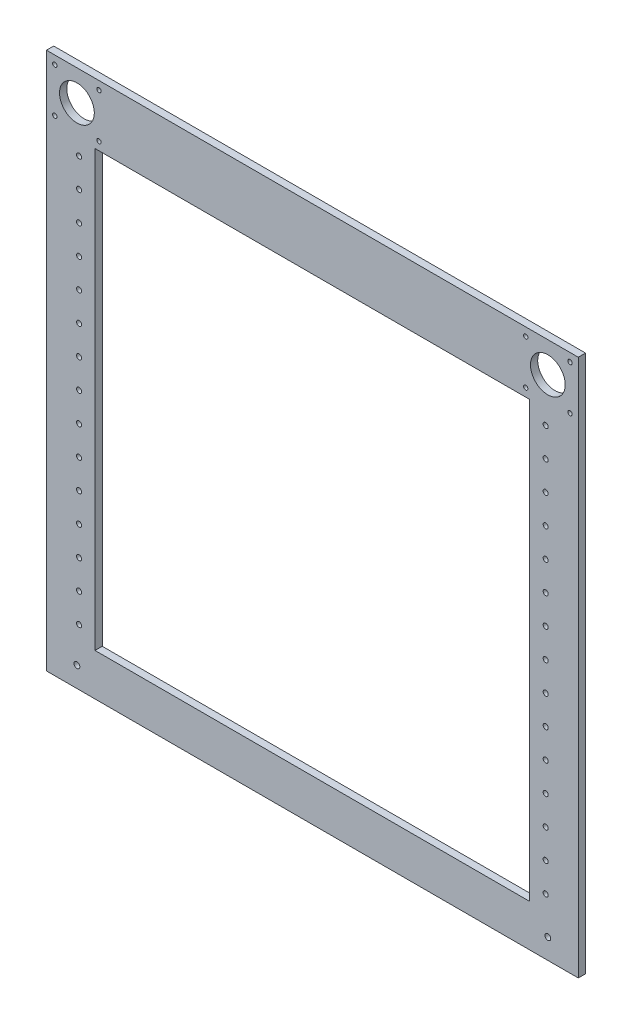
SolidWorks part; units mm, degrees
ref_plane "Front Plane" through (0, 0, 0) normal (0, 0, 1) x (1, 0, 0)
ref_plane "Top Plane" through (0, 0, 0) normal (0, 1, 0) x (1, 0, 0)
ref_plane "Right Plane" through (0, 0, 0) normal (1, 0, 0) x (0, 0, -1)
sketch "Sketch2" plane through (0, 0, -4) normal (0, 0, 1) x (1, 0, 0)
  line L1 (-7.5, -500) -> (-7.5, -200) construction
  line L2 (-307.5, -200) -> (-307.5, -500) construction
  line L4 (16, -158) -> (16, -529)
  line L5 (-7.5, -500) -> (-7.5, -200)
  line L6 (-307.5, -200) -> (-307.5, -500)
  line L7 (-331, -529) -> (-331, -158)
  line L8 (-7.5, -200) -> (-307.5, -200)
  line L9 (-7.5, -500) -> (-307.5, -500)
  line L10 (-331, -158) -> (16, -158)
  line L11 (-331, -529) -> (16, -529)
  dimension "D1" = 300
  dimension "D2" = 300
  dimension "D3" = 29
  dimension "D4" = 42
  dimension "D5" = 23.5
  dimension "D6" = 23.5
extrude "Boss-Extrude1" add sketch "Sketch2" along normal blind 5
sketch "Sketch3" plane through (0, 0, -4) normal (0, 0, -1) x (-1, 0, 0)
  line L4 (-16, -158) -> (-16, -529)
  line L5 (-16, -529) -> (331, -529)
  line L6 (331, -529) -> (331, -158)
  line L7 (331, -158) -> (-16, -158)
  line L8 (-16, -158) -> (-16, -529)
  line L9 (-16, -529) -> (331, -529)
  line L10 (331, -529) -> (331, -158)
  line L11 (331, -158) -> (-16, -158)
  circle A0 centre (320, -179) radius 12
  dimension "D2" = 24
  dimension "D1" = 0
sketch "Sketch6" plane through (0, 0, -4) normal (0, 0, -1) x (-1, 0, 0)
  circle A0 centre (318.5, -490) radius 1.75
  circle A1 centre (318.5, -470) radius 1.75
  circle A2 centre (318.5, -450) radius 1.75
  circle A3 centre (318.5, -430) radius 1.75
  circle A4 centre (318.5, -410) radius 1.75
  circle A5 centre (318.5, -390) radius 1.75
  circle A6 centre (318.5, -370) radius 1.75
  circle A7 centre (318.5, -350) radius 1.75
  circle A8 centre (318.5, -330) radius 1.75
  circle A9 centre (318.5, -310) radius 1.75
  circle A10 centre (318.5, -290) radius 1.75
  circle A11 centre (318.5, -270) radius 1.75
  circle A12 centre (318.5, -250) radius 1.75
  circle A13 centre (318.5, -230) radius 1.75
  circle A14 centre (318.5, -210) radius 1.75
  dimension "D1" = 15
extrude "Cut-Extrude1" cut sketch "Sketch6" against normal blind 10
ref_plane "Plane1" through (-157.5, 0, 0) normal (-1, 0, 0) x (0, 0, 1)
mirror "Mirror1" about plane through (-157.5, 0, 0) normal (-1, 0, 0) of "Cut-Extrude1"
sketch "Sketch7" plane through (0, 0, 1) normal (0, 0, 1) x (1, 0, 0)
  line L0 (-331, -529) -> (-331, -158) construction
  line L1 (-331, -529) -> (-331, -158)
  line L2 (-331, -158) -> (-341, -158)
  line L3 (-341, -158) -> (-341, -529)
  line L4 (-331, -529) -> (-341, -529)
  dimension "D1" = 10
extrude "Boss-Extrude2" add sketch "Sketch7" against normal blind 5
mirror "Mirror2" about plane through (-157.5, 0, 0) normal (-1, 0, 0) of "Boss-Extrude2"
extrude "Cut-Extrude2" cut sketch "Sketch3" against normal blind 5 contours A0
sketch "Sketch8" plane through (0, 0, 1) normal (0, 0, 1) x (1, 0, 0)
  line L4 (-341, -529) -> (26, -529)
  line L5 (26, -529) -> (26, -158)
  line L6 (26, -158) -> (-341, -158)
  line L7 (-341, -158) -> (-341, -529)
  line L8 (-341, -529) -> (26, -529)
  line L9 (26, -529) -> (26, -158)
  line L10 (26, -158) -> (-341, -158)
  line L11 (-341, -158) -> (-341, -529)
  dimension "D1" = 0
sketch "Sketch9" plane through (0, 0, -4) normal (0, 0, -1) x (-1, 0, 0)
  line L1 (304.7336, -163.7336) -> (335.2664, -163.7336)
  line L2 (304.7336, -163.7336) -> (304.7336, -194.2664)
  line L3 (304.7336, -194.2664) -> (335.2664, -194.2664)
  line L4 (341, -158) -> (-26, -158)
  line L5 (-26, -158) -> (-26, -529)
  line L6 (-26, -529) -> (341, -529)
  line L7 (341, -529) -> (341, -158)
  line L8 (341, -158) -> (-26, -158)
  line L9 (-26, -158) -> (-26, -529)
  line L10 (-26, -529) -> (341, -529)
  line L11 (341, -529) -> (341, -158)
  line L12 (335.2664, -163.7336) -> (335.2664, -194.2664)
  line L13 (304.7336, -163.7336) -> (335.2664, -194.2664) construction
  line L14 (304.7336, -194.2664) -> (335.2664, -163.7336) construction
  circle A0 centre (335.2664, -194.2664) radius 1.5
  circle A1 centre (335.2664, -163.7336) radius 1.5
  circle A2 centre (304.7336, -163.7336) radius 1.5
  circle A3 centre (304.7336, -194.2664) radius 1.5
  point P6 (320, -179)
  dimension "D2" = 3
  dimension "D1" = 0
extrude "Cut-Extrude3" cut sketch "Sketch9" against normal through all contours A1 | A0 | A3 | A2
mirror "Mirror3" about plane through (-157.5, 0, 0) normal (-1, 0, 0) of "Cut-Extrude2", "Cut-Extrude3"
sketch "Sketch10" plane through (0, 0, 1) normal (0, 0, 1) x (1, 0, 0)
  line L0 (-320, -179) -> (-320, -515)
  line L1 (-318.5, -210) -> (-332.4376, -210)
  circle A1 centre (-318.5, -490) radius 1.75 construction
  circle A2 centre (-320, -515) radius 2
  dimension "D1" = 25
  dimension "D2" = 4
extrude "Cut-Extrude4" cut sketch "Sketch10" against normal blind 5 contours A2
mirror "Mirror4" about plane through (-157.5, 0, 0) normal (-1, 0, 0) of "Cut-Extrude4"
